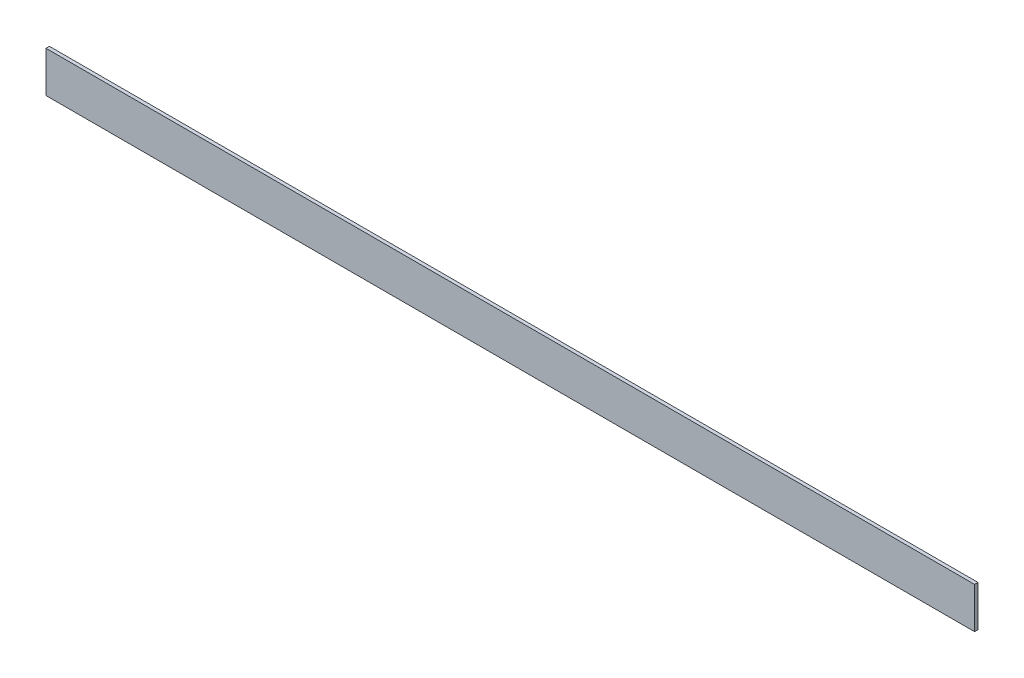
SolidWorks part; units mm, degrees
material "PVC 0.007 Plasticized"
ref_plane "Front Plane" through (0, 0, 0) normal (0, 0, 1) x (1, 0, 0)
ref_plane "Top Plane" through (0, 0, 0) normal (0, 1, 0) x (1, 0, 0)
ref_plane "Right Plane" through (0, 0, 0) normal (1, 0, 0) x (0, 0, -1)
sketch "Sketch1" plane through (0, 0, 0) normal (1, 0, 0) x (0, 0, -1)
  line L1 (-3.175, -38.1) -> (3.175, -38.1)
  line L2 (-3.175, -38.1) -> (-3.175, 38.1)
  line L3 (-3.175, 38.1) -> (3.175, 38.1)
  line L4 (3.175, -38.1) -> (3.175, 38.1)
  line L5 (-3.175, -38.1) -> (3.175, 38.1) construction
  line L6 (-3.175, 38.1) -> (3.175, -38.1) construction
  point P0 (0, 0)
  dimension "D1" = 76.2
  dimension "D2" = 6.35
extrude "Boss-Extrude1" add sketch "Sketch1" along normal blind 1727.2
equation "\"D2@Sketch1\"=1in/4"
